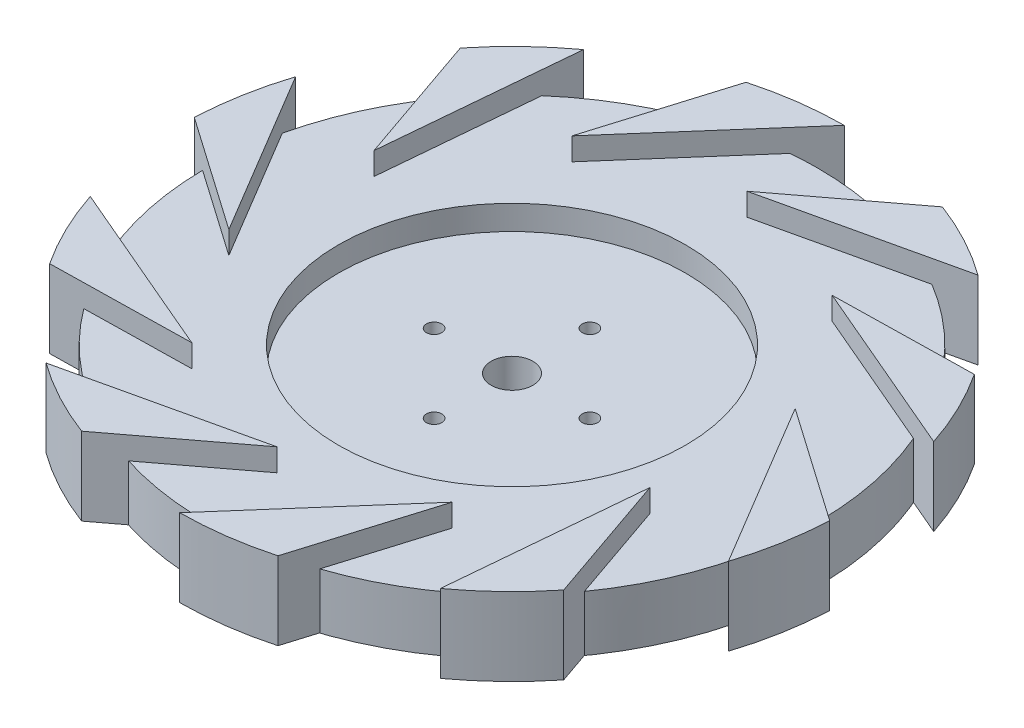
SolidWorks part; units mm, degrees
ref_plane "Front Plane" through (0, 0, 0) normal (0, 0, 1) x (1, 0, 0)
ref_plane "Top Plane" through (0, 0, 0) normal (0, 1, 0) x (1, 0, 0)
ref_plane "Right Plane" through (0, 0, 0) normal (1, 0, 0) x (0, 0, -1)
sketch "Sketch3" plane through (0, 0, 0) normal (0, 0, 1) x (1, 0, 0)
  line L0 (0, 0) -> (0, 40.1505) construction
  line L1 (-69.85, 16.0734) -> (-39.624, 16.0734)
  line L2 (-39.624, 16.0734) -> (-39.624, 10.4854)
  line L3 (-39.624, 10.4854) -> (0, 10.4854)
  line L4 (0, 10.4854) -> (0, 3.3734)
  line L5 (0, 3.3734) -> (-69.85, 3.3734)
  line L6 (-69.85, 3.3734) -> (-69.85, 16.0734)
  dimension "D1" = 12.7
  dimension "D2" = 69.85
  dimension "D3" = 39.624
  dimension "D4" = 5.588
revolve "Body" add sketch "Sketch3" angle 360 about L0
sketch "Sketch4" plane through (0, 0, 0) normal (0, 1, 0) x (1, 0, 0)
  line L0 (1.5533, 52.0769) -> (26.9502, 71.275)
  line L2 (44.4909, 61.8627) -> (1.5533, 52.0769)
  circle A1 centre (0, 0) radius 76.2 construction
  arc A3 (26.9502, 71.275) -> (44.4909, 61.8627) centre (0, 0) cw
extrude "Guide Vanes" add sketch "Sketch4" along direction (0, 1, 0) on the side of the normal blind 15.24 and the other way blind 2.54 from offset 5.969
pattern_circular "CirPattern4" count 10 over 360 about axis through (0, 0, 0) along (0, 1, 0) of "Guide Vanes"
sketch "Sketch5" plane through (0, 3.3734, 0) normal (0, -1, 0) x (1, 0, 0)
  circle A0 centre (0, 0) radius 60.325
  dimension "D1" = 120.65
sketch "Sketch6" plane through (0, 0, 0) normal (0, 1, 0) x (1, 0, 0)
  circle A0 centre (0, 17.78) radius 1.7526
  dimension "D1" = 3.5052
  dimension "D2" = 17.78
extrude "Cut-Extrude1" cut sketch "Sketch6" along normal blind 13.97
pattern_circular "CirPattern5" count 4 over 360 about axis through (0, 0, 0) along (0, 1, 0) of "Cut-Extrude1"
sketch "Sketch9" plane through (0, 10.4854, 0) normal (0, 1, 0) x (1, 0, 0)
  circle A0 centre (0, 0) radius 4.7625
  dimension "D1" = 9.525
extrude "Cut-Extrude2" cut sketch "Sketch9" against normal blind 7.62
sketch "Sketch8" plane through (0, 0, 0) normal (0, 1, 0) x (1, 0, 0)
  circle A0 centre (0, 0) radius 76.2 construction
